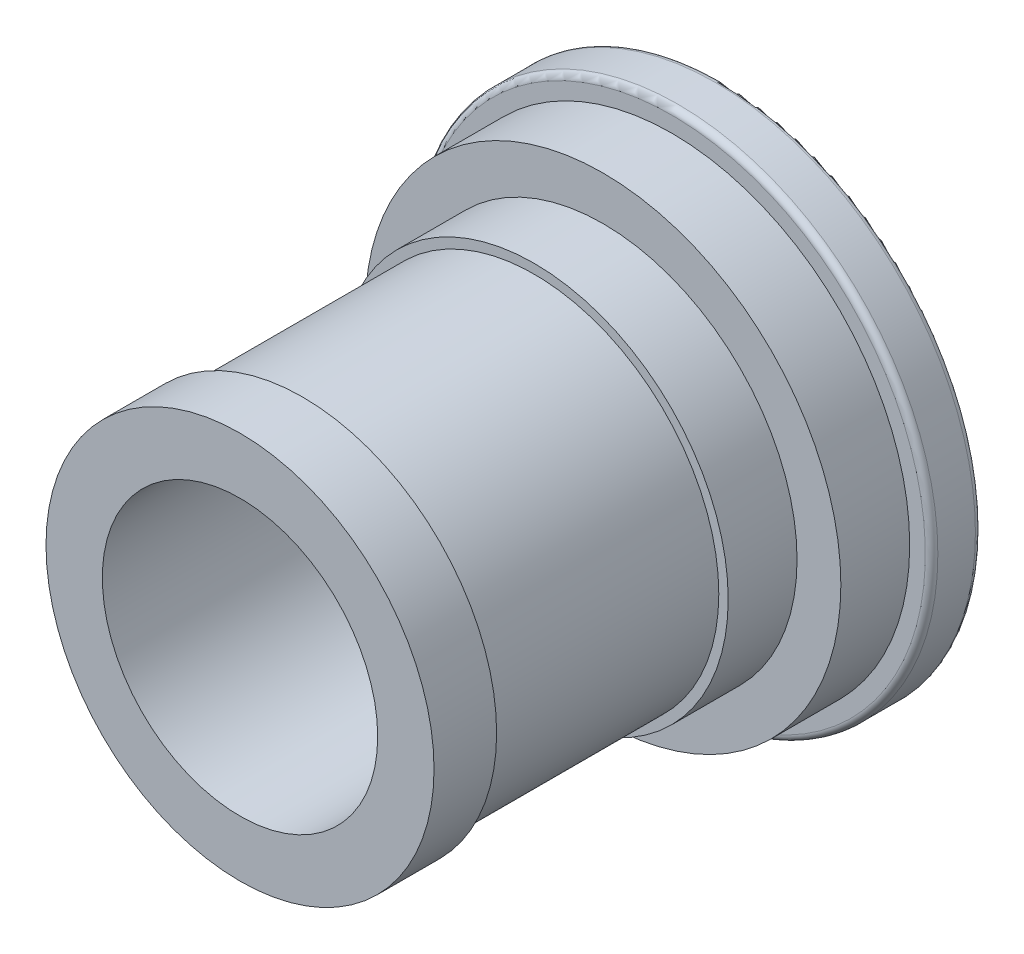
SolidWorks part; units mm, degrees
ref_plane "Front Plane" through (0, 0, 0) normal (0, 0, 1) x (1, 0, 0)
ref_plane "Top Plane" through (0, 0, 0) normal (0, 1, 0) x (1, 0, 0)
ref_plane "Right Plane" through (0, 0, 0) normal (1, 0, 0) x (0, 0, -1)
sketch "Sketch1" plane through (0, 0, 0) normal (0, 1, 0) x (1, 0, 0)
  line L0 (0, 0) -> (0, 128.5958) construction
  line L1 (-41.5, 77) -> (-22, 77)
  line L2 (-31, 0) -> (-31, 10)
  line L3 (-31, 10) -> (-29.5, 10)
  line L4 (-29.5, 10) -> (-29.5, 47)
  line L5 (-29.5, 47) -> (-31, 47)
  line L6 (-31, 47) -> (-31, 58)
  line L7 (-31, 58) -> (-38, 58)
  line L8 (-38, 58) -> (-38, 69)
  line L9 (-38, 69) -> (-41.5, 69)
  line L10 (-41.5, 69) -> (-41.5, 77)
  line L11 (-22, 77) -> (-22, 0)
  line L13 (-22, 0) -> (-31, 0)
  dimension "D2" = 11
  dimension "D3" = 11
  dimension "D4" = 8
  dimension "D5" = 10
  dimension "D6" = 62
  dimension "D7" = 59
  dimension "D8" = 83
  dimension "D9" = 76
  dimension "D10" = 62
  dimension "D11" = 77
  dimension "D12" = 44
revolve "Revolve1" add sketch "Sketch1" angle 360 about L0
fillet "Fillet2" radius 1 2 edges at (41.5, 0, -69) (41.5, 0, -77)
